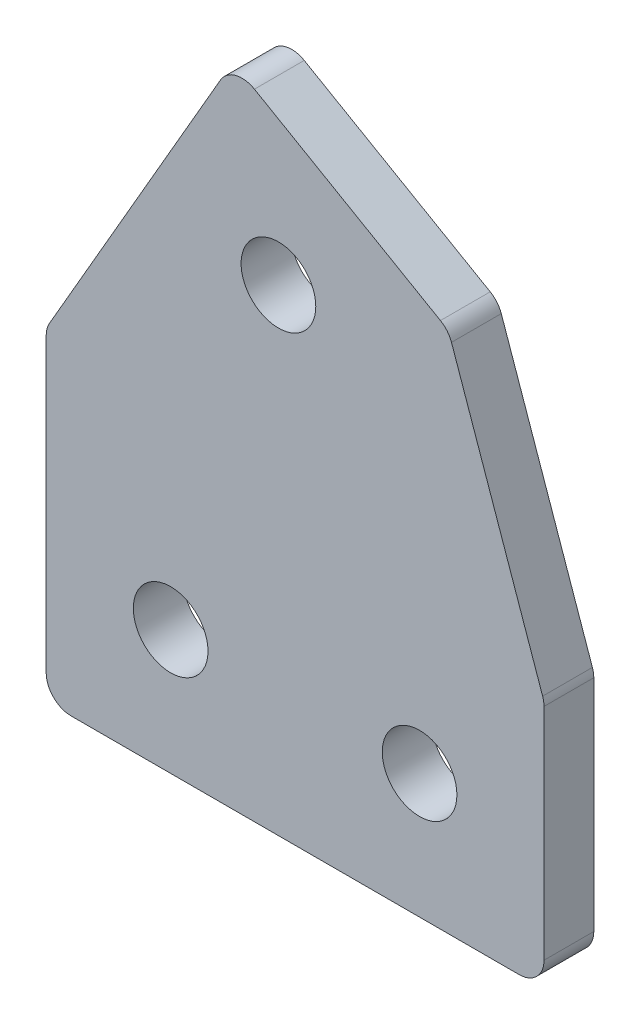
SolidWorks part; units mm, degrees
material "环氧板3240"
ref_plane "前视基准面" through (0, 0, 0) normal (0, 0, 1) x (1, 0, 0)
ref_plane "上视基准面" through (0, 0, 0) normal (0, 1, 0) x (1, 0, 0)
ref_plane "右视基准面" through (0, 0, 0) normal (1, 0, 0) x (0, 0, -1)
other "Configuration Table"
sketch "草图1" plane through (0, 0, 0) normal (0, 0, 1) x (1, 0, 0)
  line L0 (-133.2406, -50.9842) -> (-133.2406, -37.9842)
  line L1 (-133.2406, -37.9842) -> (-125.7406, -24.9938)
  line L2 (-125.7406, -24.9938) -> (-117.0804, -29.9938)
  line L3 (-117.0804, -29.9938) -> (-123.2406, -40.6637) construction
  line L4 (-123.2406, -40.6637) -> (-123.2406, -50.9842) construction
  line L5 (-123.2406, -50.9842) -> (-133.2406, -50.9842)
  line L6 (-128.2406, -50.9842) -> (-128.2406, -39.324) construction
  line L7 (-128.2406, -39.324) -> (-121.4105, -27.4938) construction
  line L8 (-123.2406, -50.9842) -> (-117.0804, -29.9938) construction
  line L10 (-123.9105, -31.824) -> (-119.5804, -34.324) construction
  line L14 (-113.2406, -50.9842) -> (-113.2406, -40.9842)
  line L15 (-128.2406, -45.9842) -> (-118.2406, -45.9842) construction
  line L17 (-123.2406, -50.9842) -> (-113.2406, -50.9842)
  line L19 (-113.2406, -50.9842) -> (-117.0804, -29.9938) construction
  line L20 (-113.2406, -40.9842) -> (-117.0804, -29.9938)
  circle A0 centre (-128.2406, -45.9842) radius 1.5
  circle A1 centre (-123.9105, -31.824) radius 1.5
  circle A7 centre (-118.2406, -45.9842) radius 1.5
  point P13 (-113.1699, -50.9842)
  dimension "D4" = 3
  dimension "D5" = 10
  dimension "D8" = 5
  dimension "D9" = 10
  dimension "D7" = 10
  dimension "D6" = 8
  dimension "D13" = 5
  dimension "D1" = 150
  dimension "D2" = 10
  dimension "D3" = 10
  dimension "D12" = 5
extrude "凸台-拉伸1" add sketch "草图1" along normal blind 2
fillet "圆角1" radius 1 6 edges at (-133.2406, -37.9842, 1) (-133.2406, -50.9842, 1) (-125.7406, -24.9938, 1) (-117.0804, -29.9938, 1) (-113.2406, -40.9842, 1) (-113.2406, -50.9842, 1)
